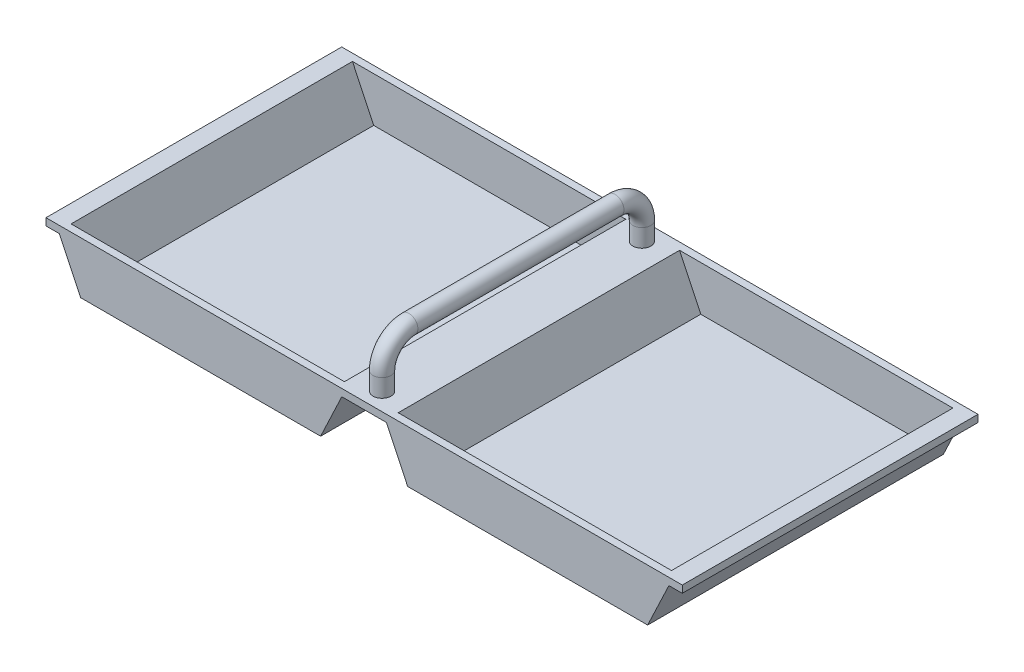
SolidWorks part; units mm, degrees
ref_plane "Front Plane" through (0, 0, 0) normal (0, 0, 1) x (1, 0, 0)
ref_plane "Top Plane" through (0, 0, 0) normal (0, 1, 0) x (1, 0, 0)
ref_plane "Right Plane" through (0, 0, 0) normal (1, 0, 0) x (0, 0, -1)
sketch "Sketch2" plane through (0, 0, 0) normal (0, 0, 1) x (1, 0, 0)
  line L0 (-177.5, 0) -> (-167.5, 0)
  line L1 (-167.5, 0) -> (-155.6569, -25)
  line L2 (-155.6569, -25) -> (-26.8169, -25)
  line L3 (-26.8169, -25) -> (-15, 0)
  line L4 (0, 0) -> (0, 95.7647) construction
  line L5 (26.8169, -25) -> (15, 0)
  line L6 (155.6569, -25) -> (26.8169, -25)
  line L7 (167.5, 0) -> (155.6569, -25)
  line L8 (-15, 0) -> (15, 0)
  line L9 (167.5, 0) -> (177.5, 0)
  point P4 (0, 0)
  dimension "D1" = 355
  dimension "D2" = 10
  dimension "D3" = 25
  dimension "D4" = 27.6633
  dimension "D5" = 10
  dimension "D6" = 128.84
  dimension "D7" = 30
  dimension "D8" = 177.5
  dimension "D9" = 177.5
extrude "Extrude-Thin2" add sketch "Sketch2" along normal mid plane 157 thin
sketch "Sketch5" plane through (0, 0, 78.5) normal (0, 0, 1) x (1, 0, 0)
  line L0 (-177.5, 0) -> (177.5, 0)
  line L1 (177.5, 0) -> (177.5, -4)
  line L2 (177.5, 0) -> (177.5, -4) construction
  line L3 (177.5, -4) -> (170.0312, -4)
  line L4 (170.0312, -4) -> (158.1881, -29)
  line L5 (158.1881, -29) -> (24.2832, -29)
  line L6 (24.2832, -29) -> (12.4664, -4)
  line L7 (12.4664, -4) -> (-12.4664, -4)
  line L8 (-12.4664, -4) -> (-24.2832, -29)
  line L9 (-24.2832, -29) -> (-158.1881, -29)
  line L10 (-158.1881, -29) -> (-170.0312, -4)
  line L11 (-170.0312, -4) -> (-177.5, -4)
  line L12 (-177.5, -4) -> (-177.5, 0)
extrude "Boss-Extrude1" add sketch "Sketch5" along normal blind 4
sketch "Sketch6" plane through (0, 0, -78.5) normal (0, 0, -1) x (-1, 0, 0)
  line L0 (-177.5, 0) -> (-177.5, -4)
  line L1 (-177.5, -4) -> (-170.0312, -4)
  line L2 (-170.0312, -4) -> (-158.1881, -29)
  line L3 (-158.1881, -29) -> (-24.2832, -29)
  line L4 (-24.2832, -29) -> (-12.4664, -4)
  line L5 (-12.4664, -4) -> (12.4664, -4)
  line L6 (12.4664, -4) -> (24.2832, -29)
  line L7 (24.2832, -29) -> (158.1881, -29)
  line L8 (158.1881, -29) -> (170.0312, -4)
  line L9 (170.0312, -4) -> (177.5, -4)
  line L10 (177.5, -4) -> (177.5, 0)
  line L11 (177.5, 0) -> (-177.5, 0)
extrude "Boss-Extrude2" add sketch "Sketch6" along normal blind 4
sketch "Sketch8" plane through (0, 0, 0) normal (1, 0, 0) x (0, 0, -1)
  line L0 (-67.5, 0) -> (-67.5, 10)
  line L1 (-82.5, 0) -> (82.5, 0) construction
  line L2 (-57.5, 20) -> (57.5, 20)
  line L3 (67.5, 10) -> (67.5, 0)
  arc A0 (-57.5, 20) -> (-67.5, 10) centre (-57.5, 10) ccw
  arc A1 (57.5, 20) -> (67.5, 10) centre (57.5, 10) cw
  dimension "D1" = 15
  dimension "D4" = 10
  dimension "D2" = 15
  dimension "D3" = 20
  dimension "D5" = 10
  dimension "D6" = 10
  dimension "D7" = 10
sketch "Sketch10" plane through (0, 0, 0) normal (0, 0, 1) x (1, 0, 0)
  line L0 (0, 10) -> (0, 20) construction
  line L1 (0, 10) -> (0, 20) construction
  circle A1 centre (0, 25) radius 5
  dimension "D2" = 10
  dimension "D3" = 25
sweep "Sweep2" add profiles "Sketch10" path "Sketch8"
mirror "Mirror2" about plane through (0, 0, 0) normal (0, 0, 1) of "Sweep2"
